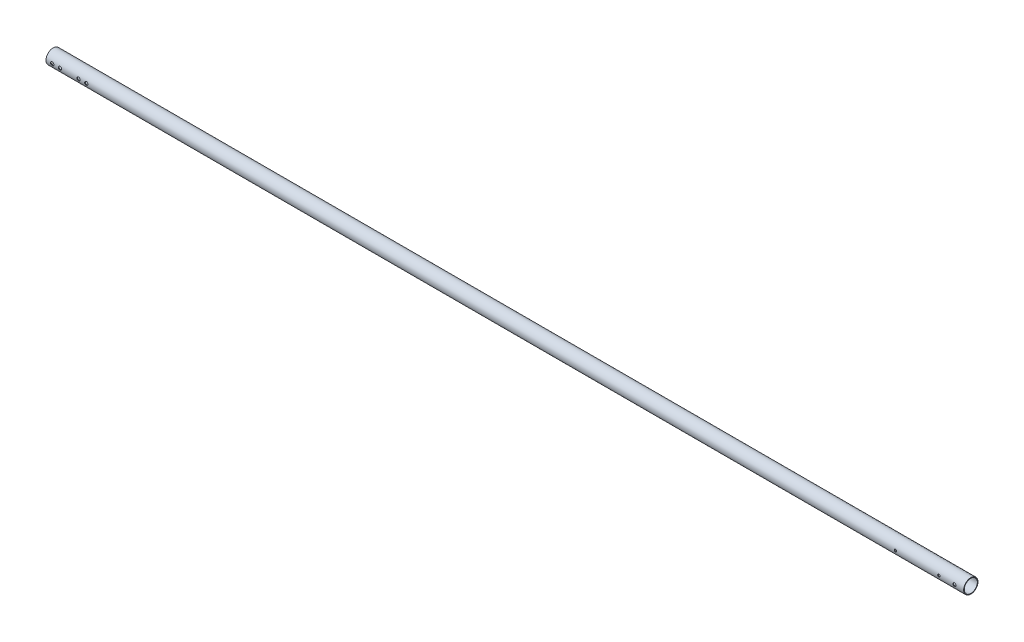
SolidWorks part; units mm, degrees
material "Galvanized Steel"
ref_plane "Front Plane" through (0, 0, 0) normal (0, 0, 1) x (1, 0, 0)
ref_plane "Top Plane" through (0, 0, 0) normal (0, 1, 0) x (1, 0, 0)
ref_plane "Right Plane" through (0, 0, 0) normal (1, 0, 0) x (0, 0, -1)
sketch "Sketch1" plane through (0, 0, 0) normal (1, 0, 0) x (0, 0, -1)
  circle A0 centre (0, 0) radius 14.732
  circle A1 centre (0, 0) radius 13.3858
  dimension "D1" = 29.464
  dimension "D2" = 26.7716
extrude "Boss-Extrude1" add sketch "Sketch1" along normal blind 1881.1875
sketch "Sketch2" plane through (0, 0, 0) normal (0, 0, 1) x (1, 0, 0)
  line L0 (1881.1875, -14.732) -> (1881.1875, 14.732) construction
  circle A2 centre (1830.3875, 0) radius 2.4638
  circle A3 centre (1741.4875, 0) radius 2.4638
  circle A4 centre (1862.1375, 0) radius 3.175
  dimension "D1" = 4.9276
  dimension "D2" = 50.8
  dimension "D3" = 139.7
  dimension "D7" = 19.05
extrude "Cut-Extrude2" cut sketch "Sketch2" against normal through all both and the other way through all
sketch "Sketch3" plane through (0, 0, 0) normal (0, 0, 1) x (1, 0, 0)
  line L0 (0, 14.732) -> (0, -14.732) construction
  circle A0 centre (12.7, 0) radius 3.3655
  circle A1 centre (28.575, 0) radius 3.3655
  dimension "D3" = 6.731
  dimension "D1" = 12.7
  dimension "D2" = 28.575
extrude "Cut-Extrude3" cut sketch "Sketch3" against normal through all both and the other way through all
pattern_linear "LPattern1" count 2 spacing 53.975 along (1, 0, 0) of "Cut-Extrude3"
